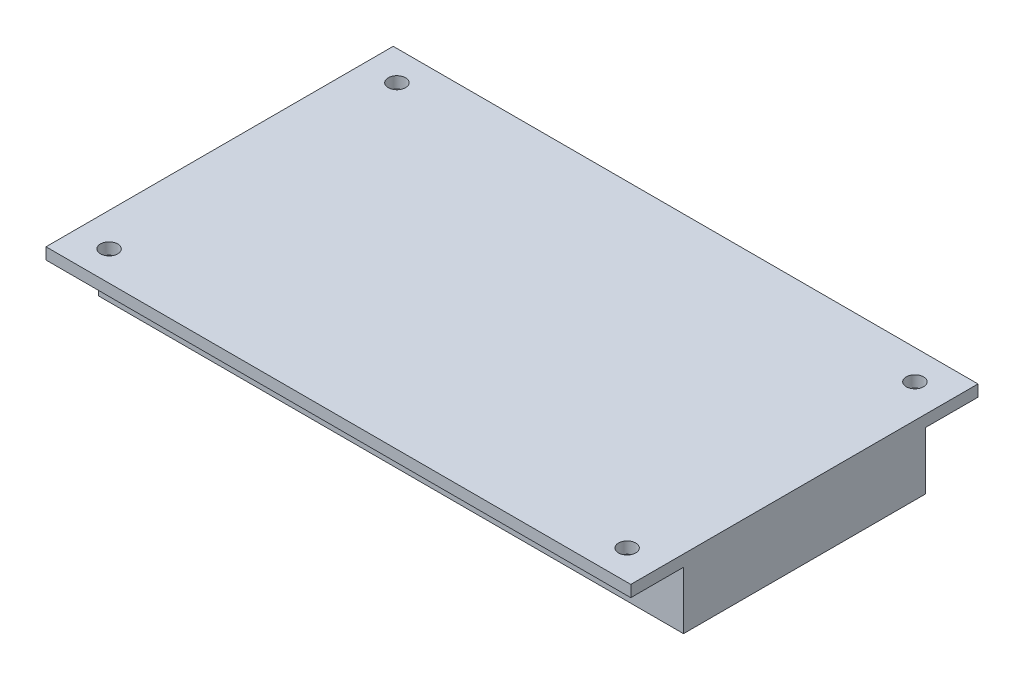
SolidWorks part; units mm, degrees
ref_plane "Front Plane" through (0, 0, 0) normal (0, 0, 1) x (1, 0, 0)
ref_plane "Top Plane" through (0, 0, 0) normal (0, 1, 0) x (1, 0, 0)
ref_plane "Right Plane" through (0, 0, 0) normal (1, 0, 0) x (0, 0, -1)
sketch "Sketch1" plane through (0, 0, 0) normal (0, 1, 0) x (1, 0, 0)
  line L1 (50.8, 30.1625) -> (-50.8, 30.1625)
  line L2 (50.8, 30.1625) -> (50.8, -30.1625)
  line L3 (50.8, -30.1625) -> (-50.8, -30.1625)
  line L4 (-50.8, 30.1625) -> (-50.8, -30.1625)
  line L5 (50.8, 30.1625) -> (-50.8, -30.1625) construction
  line L6 (50.8, -30.1625) -> (-50.8, 30.1625) construction
  point P0 (0, 0)
  dimension "D1" = 101.6
  dimension "D2" = 60.325
extrude "Boss-Extrude1" add sketch "Sketch1" along normal blind 12
sketch "Sketch2" plane through (50.8, 0, 0) normal (1, 0, 0) x (0, 0, -1)
  line L0 (0, 0) -> (0, 50000) construction
  line L1 (-30.1625, 0) -> (-21, 0)
  line L2 (-30.1625, 0) -> (-30.1625, 10)
  line L3 (-30.1625, 10) -> (-21, 10)
  line L4 (-21, 0) -> (-21, 10)
  line L5 (30.1625, 0) -> (21, 0)
  line L6 (30.1625, 0) -> (30.1625, 10)
  line L7 (30.1625, 10) -> (21, 10)
  line L8 (21, 0) -> (21, 10)
  line L9 (-30.1625, 0) -> (30.1625, 0) construction
  point P14 (0, 0)
  dimension "D1" = 42
  dimension "D2" = 10
extrude "Cut-Extrude1" cut sketch "Sketch2" against normal through all
sketch "Sketch3" plane through (0, 12, 0) normal (0, 1, 0) x (1, 0, 0)
  line L0 (0, 0) -> (0, 50000) construction
  line L1 (0, 0) -> (50000, 0) construction
  circle A0 centre (-45, 25) radius 1.5
  circle A1 centre (-45, -25) radius 1.5
  circle A2 centre (45, -25) radius 1.5
  circle A3 centre (45, 25) radius 1.5
  dimension "D2" = 3
  dimension "D1" = 90
  dimension "D3" = 50
extrude "Cut-Extrude2" cut sketch "Sketch3" against normal through all
